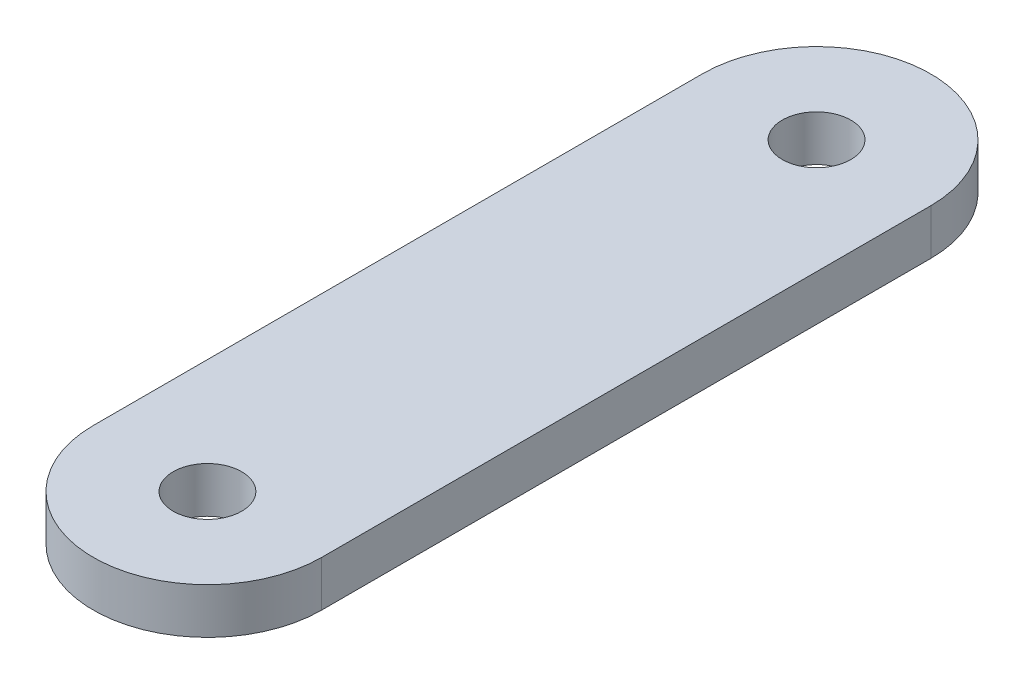
SolidWorks part; units mm, degrees
ref_plane "Front Plane" through (0, 0, 0) normal (0, 0, 1) x (1, 0, 0)
ref_plane "Top Plane" through (0, 0, 0) normal (0, 1, 0) x (1, 0, 0)
ref_plane "Right Plane" through (0, 0, 0) normal (1, 0, 0) x (0, 0, -1)
sketch "Sketch1" plane through (0, 0, 0) normal (0, 1, 0) x (1, 0, 0)
  line L0 (-7.5, 40) -> (-7.5, 0)
  line L1 (7.5, 40) -> (7.5, 0)
  arc A0 (-7.5, 0) -> (7.5, 0) centre (0, 0) ccw
  circle A1 centre (0, 0) radius 2.25
  arc A2 (7.5, 40) -> (-7.5, 40) centre (0, 40) ccw
  circle A3 centre (0, 40) radius 2.25
  dimension "D1" = 15
  dimension "D2" = 4.5
  dimension "D3" = 4.5
  dimension "D4" = 40
extrude "Boss-Extrude1" add sketch "Sketch1" along normal blind 3
